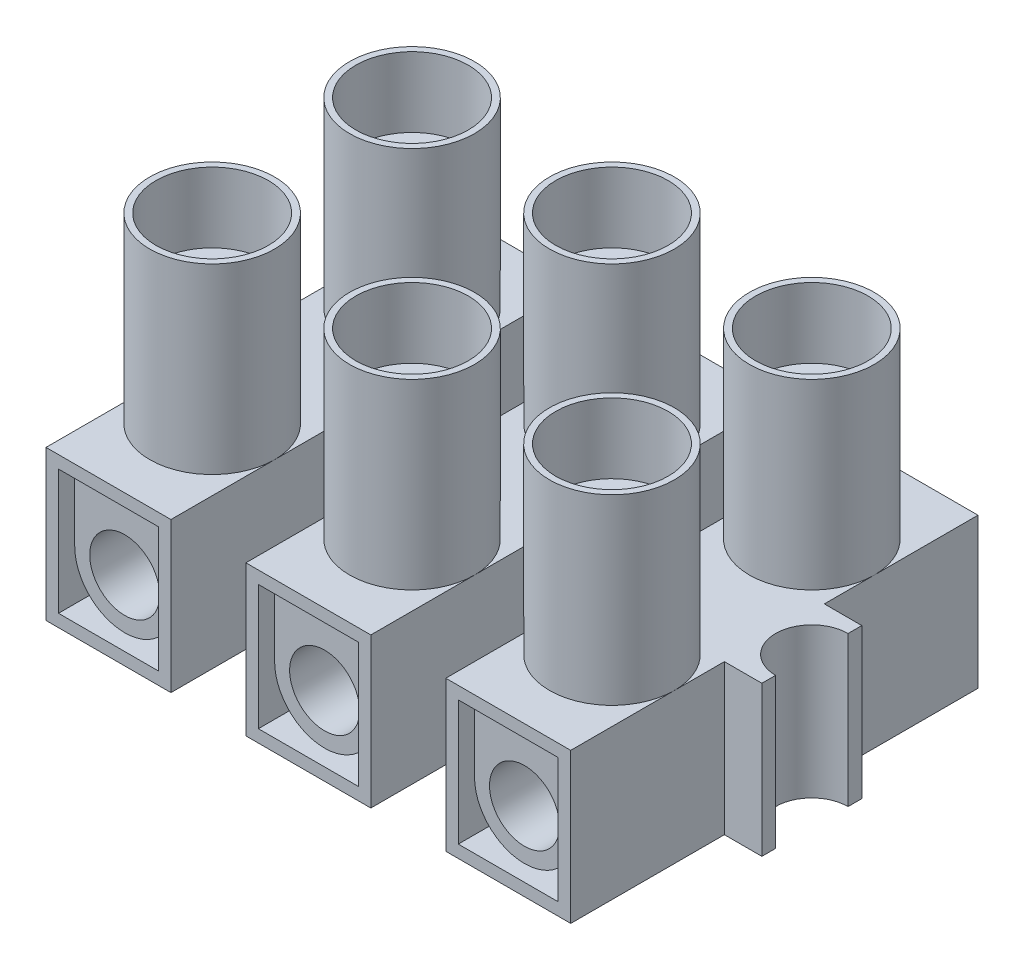
SolidWorks part; units mm, degrees
ref_plane "Plan de face" through (0, 0, 0) normal (0, 0, 1) x (1, 0, 0)
ref_plane "Plan de dessus" through (0, 0, 0) normal (0, 1, 0) x (1, 0, 0)
ref_plane "Plan de droite" through (0, 0, 0) normal (1, 0, 0) x (0, 0, -1)
sketch "Esquisse1" plane through (0, 0, 0) normal (0, 0, 1) x (1, 0, 0)
  line L1 (-2.5, 3) -> (2.5, 3)
  line L2 (-2.5, 3) -> (-2.5, -3)
  line L3 (-2.5, -3) -> (2.5, -3)
  line L4 (2.5, 3) -> (2.5, -3)
  line L5 (-2.5, 3) -> (2.5, -3) construction
  line L6 (-2.5, -3) -> (2.5, 3) construction
  line L7 (-2, 2.5) -> (2, 2.5)
  line L8 (-2, 2.5) -> (-2, -2.5)
  line L9 (-2, -2.5) -> (2, -2.5)
  line L10 (2, 2.5) -> (2, -2.5)
  line L11 (-2, 2.5) -> (2, -2.5) construction
  line L12 (-2, -2.5) -> (2, 2.5) construction
  point P0 (0, 0)
  point P6 (0, 0)
  dimension "D1" = 5
  dimension "D2" = 6
  dimension "D3" = 0.5
  dimension "D4" = 0.5
extrude "Boss.-Extru.1" add sketch "Esquisse1" along normal mid plane 16.3
sketch "Esquisse2" plane through (0, -3, 0) normal (0, -1, 0) x (1, 0, 0)
  line L0 (0, 4) -> (0, -4) construction
  line L1 (2.5, 8.15) -> (2.5, -8.15) construction
  circle A0 centre (0, 4) radius 2.5
  circle A1 centre (0, -4) radius 2.5
  circle A2 centre (0, 4) radius 2.25
  circle A3 centre (0, -4) radius 2.25
  point P4 (0, 0)
  dimension "D2" = 4.5
  dimension "D1" = 8
extrude "Boss.-Extru.2" add sketch "Esquisse2" against normal offset from surface (7.3 mm away) 13.3 from surface at -6 up to face at (0, -3, 0) starting at face at (0, 3, 0)
sketch "Esquisse3" plane through (0, 3, 0) normal (0, 1, 0) x (1, 0, 0)
  line L0 (-2.5, 2) -> (-4, 2)
  line L1 (-2.5, -4) -> (-2.5, 4) construction
  line L2 (-4, 2) -> (-4, 1.45)
  line L3 (-4, -1.45) -> (-4, -2)
  line L4 (-4, -2) -> (-2.5, -2)
  line L5 (-2.5, -2) -> (-2.5, 2)
  arc A0 (-4, 1.45) -> (-4, -1.45) centre (-4, 0) cw
  dimension "D1" = 1.45
  dimension "D2" = 4
  dimension "D3" = 4
extrude "Boss.-Extru.3" add sketch "Esquisse3" against normal up to vertex (6 mm away) up to point (-2.5, -3, 8.15)
mirror "Symétrie1" about plane through (0, 0, 0) normal (1, 0, 0) of "Boss.-Extru.3"
sketch "Esquisse4" plane through (0, 0, 0) normal (0, 0, 1) x (1, 0, 0)
  line L2 (-2, -2.5) -> (2, -2.5) construction
  line L3 (2, -2.5) -> (2, 2.5) construction
  line L4 (-2, 2.5) -> (-2, -2.5) construction
  line L5 (-2, 2.5) -> (-2, -0.5)
  line L6 (2, -0.5) -> (2, 2.5)
  line L7 (-2, 2.5) -> (2, 2.5)
  line L8 (2, 2.5) -> (-2, 2.5) construction
  circle A0 centre (0, -0.5) radius 1.4
  arc A1 (-2, -0.5) -> (2, -0.5) centre (0, -0.5) ccw
  dimension "D1" = 2.8
extrude "Boss.-Extru.4" add sketch "Esquisse4" along normal mid plane 15 separate body
sketch "Esquisse5" plane through (0, 3, 0) normal (0, 1, 0) x (1, 0, 0)
  line L0 (-2, -8.15) -> (-2, 8.15) construction
  circle A0 centre (0, -4) radius 2.25 construction
  circle A1 centre (0, 4) radius 2.25 construction
  circle A2 centre (0, -4) radius 2
  circle A4 centre (0, 4) radius 2
extrude "Enlèv. mat.-Extru.1" cut sketch "Esquisse5" against normal up to next (0.5 mm away)
hole_wizard "Trou taraudé M2.51" positions "Esquisse7" profile "Esquisse6" tap size "M2.5" standard "ISO"
sketch "Esquisse7" plane through (0, 2.5, 0) normal (0, 1, 0) x (-1, 0, 0)
  circle A0 centre (0, 4) radius 2 construction
  point P0 (0, 4)
  point P4 (0, -4)
sketch "Esquisse6" plane through (0, 2.5, 4) normal (1, 0, 0) x (0, 0, 1)
  line L0 (0, 0) -> (0, 3.1159)
  line L1 (0, 3.1159) -> (1.025, 2.5)
  line L2 (1.025, 2.5) -> (1.025, 0)
  line L5 (1.025, 0) -> (0, 0)
  line L10 (0, 3.1159) -> (-1.025, 2.5) construction
  line L11 (0, -6.35) -> (0, 107.95) construction
  dimension "Diamètre du trou pour taraudage" = 2.05
  dimension "Profondeur du trou pour taraudage" = 2.5
  dimension "Angle de pointe" = 118
cosmetic thread "Filetage de perçage1" parameters "D1"=2.0464, "D2"=2.5
cosmetic thread "Filetage de perçage2" parameters "D1"=2.0464, "D2"=2.5
sketch "Esquisse8" plane through (0, 0, 0) normal (1, 0, 0) x (0, 0, -1)
  line L0 (-4, 7.5) -> (-4, 0.5)
  line L1 (-4, 7.5) -> (-6.25, 7.5)
  line L2 (-6.25, 7.5) -> (-6.25, 5.5)
  line L3 (-6.25, 5.5) -> (-5.3, 5.5)
  line L4 (-5.3, 5.5) -> (-5.3, 0.5)
  line L5 (-5.3, 0.5) -> (-4, 0.5)
  dimension "D1" = 4
  dimension "D2" = 1.3
  dimension "D3" = 5
  dimension "D4" = 2
  dimension "D5" = 2.25
  dimension "D6" = 0.5
revolve "Révolution1" add sketch "Esquisse8" angle 360 about L0
sketch "Esquisse9" plane through (0, 0, 0) normal (1, 0, 0) x (0, 0, -1)
  line L0 (-1.75, 7.5) -> (-6.25, 7.5) construction
  line L1 (-4.3, 7.5) -> (-3.7, 7.5)
  line L2 (-4.3, 7.5) -> (-4.3, 6.9)
  line L3 (-4.3, 6.9) -> (-3.7, 6.9)
  line L4 (-3.7, 7.5) -> (-3.7, 6.9)
  line L5 (-4, 6.9) -> (-4, 5.5) construction
  line L6 (-6.25, 5.5) -> (-1.75, 5.5) construction
  dimension "D1" = 0.6
  dimension "D2" = 0.6
extrude "Enlèv. mat.-Extru.2" cut sketch "Esquisse9" against normal through all and the other way through all
mirror "Symétrie3" about plane through (0, 0, 0) normal (0, 0, 1) of bodies 111
pattern_linear "Répétition linéaire1" count 3 spacing 8 along (1, 0, 0) of bodies 112 111 107 106
combine bodies "Combiner1" operation type add bodies to combine 106 120 119
